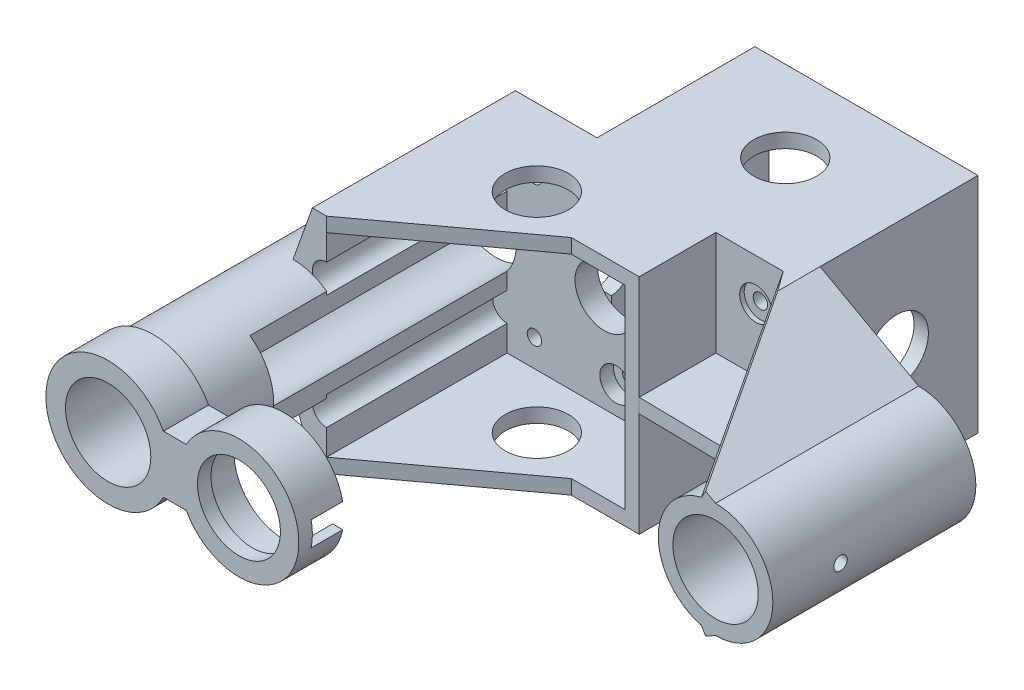
SolidWorks part; units mm, degrees
material "A-Glass Fiber"
ref_plane "Front" through (0, 0, 0) normal (0, 0, 1) x (1, 0, 0)
ref_plane "Top" through (0, 0, 0) normal (0, 1, 0) x (1, 0, 0)
ref_plane "Right" through (0, 0, 0) normal (1, 0, 0) x (0, 0, -1)
sketch "Sketch4" plane through (0, 0, 0) normal (0, 0, 1) x (1, 0, 0)
  line L0 (0, -42.8625) -> (0, 41.275) construction
  line L1 (-49.15, -15.5) -> (-80.15, 15.5) construction
  line L2 (-80.15, -15.5) -> (-49.15, 15.5) construction
  line L3 (-39.925, 44.5615) -> (-39.925, -66.5635) construction
  line L4 (-71.275, 44.5615) -> (-71.275, -66.5635) construction
  line L8 (-62.05, 15.5) -> (-31.05, -15.5) construction
  line L9 (-31.05, 15.5) -> (-62.05, -15.5) construction
  line L11 (-31.05, 36.624) -> (-31.05, -53.8635) construction
  line L12 (43.75, 0) -> (-164.4633, 0) construction
  line L13 (-62.05, 36.624) -> (-62.05, -53.8635) construction
  line L14 (-49.15, 36.624) -> (-49.15, -53.8635) construction
  line L15 (-80.15, 36.624) -> (-80.15, -53.8635) construction
  line L16 (-113.2228, 15.5) -> (-0.2036, 15.5) construction
  line L17 (-113.2228, -15.5) -> (-0.2036, -15.5) construction
  line L18 (-25, -66.5635) -> (-25, 44.5615) construction
  line L19 (-68.1, -66.5635) -> (-68.1, 44.5615) construction
  line L20 (-43.1, 44.5615) -> (-43.1, -66.5635) construction
  line L21 (-86.2, -66.5635) -> (-86.2, 44.5615) construction
  line L22 (5.8397, -21.55) -> (-134.1626, -21.55) construction
  line L23 (5.8397, 21.55) -> (-134.1626, 21.55) construction
  line L24 (10.9249, -24.725) -> (-138.6228, -24.725) construction
  line L25 (10.9249, 24.725) -> (-138.6228, 24.725) construction
  line L26 (-89.375, 44.5615) -> (-89.375, -66.5635) construction
  line L27 (-21.825, 44.5615) -> (-21.825, -66.5635) construction
  circle A0 centre (0, 0) radius 12.7 construction
  circle A1 centre (0, 0) radius 15.875 construction
  circle A2 centre (0, 0) radius 9.46 construction
  circle A3 centre (-93.65, 0) radius 9.46 construction
  arc A4 (-93.65, 12.7) -> (-93.65, -12.7) centre (-93.65, 0) ccw construction
  circle A5 centre (27.27, 0) radius 9.46 construction
  circle A6 centre (27.27, 0) radius 12.7 construction
  circle A7 centre (-120.3675, 0) radius 9.46 construction
  circle A8 centre (-120.3675, 0) radius 12.7 construction
  point P3 (0, 0)
  point P6 (-49.15, -15.5)
  point P11 (-93.65, 0)
  point P12 (-49.15, 15.5)
  point P13 (-46.55, 0)
  point P14 (-80.15, 15.5)
  point P15 (-80.15, -15.5)
  point P61 (-64.65, 0)
  point P65 (27.27, 0)
  point P66 (-120.3675, 0)
  dimension "D20" = 3.175
  dimension "D18" = 29
  dimension "D26" = 73.82
  dimension "D27" = 64.65
  dimension "D2" = 31
  dimension "D3" = 25
  dimension "D4" = 31
  dimension "D5" = 21.825
  dimension "D6" = 15.5
  dimension "D7" = 15.5
  dimension "D8" = 6.05
  dimension "D9" = 6.05
  dimension "D10" = 6.05
  dimension "D11" = 6.05
  dimension "D12" = 6.05
  dimension "D13" = 6.05
  dimension "D14" = 3.175
  dimension "D15" = 3.175
  dimension "D16" = 3.175
  dimension "D17" = 3.175
  dimension "D19" = 3.175
  dimension "D21" = 3.175
  dimension "D22" = 46.55
  dimension "D23" = 47.1
  dimension "D24" = 58.32
  dimension "D25" = 147.6375
sketch "Sketch5" plane through (0, 0, 0) normal (0, 0, 1) x (1, 0, 0)
  line L0 (-21.825, -24.725) -> (0, -12.7)
  line L1 (10.9249, -24.725) -> (-138.6228, -24.725) construction
  line L2 (-21.825, 44.5615) -> (-21.825, -66.5635) construction
  line L3 (0, -42.8625) -> (0, 41.275) construction
  line L4 (10.9249, 24.725) -> (-138.6228, 24.725) construction
  line L5 (-21.825, 24.725) -> (0, 12.7)
  line L6 (-93.65, 0) -> (-93.65, -30.9694) construction
  line L7 (-93.65, 12.7) -> (-89.375, 24.725)
  line L8 (-89.375, 44.5615) -> (-89.375, -66.5635) construction
  line L9 (-89.375, 24.725) -> (-21.825, 24.725)
  line L10 (-89.375, -24.725) -> (-93.65, -12.7)
  line L11 (-89.375, -24.725) -> (-21.825, -24.725)
  circle A0 centre (0, 0) radius 12.7 construction
  arc A1 (0, 12.7) -> (0, -12.7) centre (0, 0) cw
  circle A2 centre (0, 0) radius 9.46
  circle A3 centre (-93.65, 0) radius 9.46
  arc A4 (-93.65, 12.7) -> (-93.65, -12.7) centre (-93.65, 0) ccw
  circle A6 centre (-31.05, 15.5) radius 1.6
  circle A7 centre (-31.05, -15.5) radius 1.6
  circle A8 centre (-49.15, -15.5) radius 1.6
  circle A9 centre (-49.15, 15.5) radius 1.6
  circle A10 centre (-62.05, 15.5) radius 1.6
  circle A11 centre (-80.15, 15.5) radius 1.6
  circle A12 centre (-80.15, -15.5) radius 1.6
  circle A13 centre (-62.05, -15.5) radius 1.6
extrude "Extrude1" add sketch "Sketch5" along normal blind 5
sketch "Sketch6" plane through (0, 0, 5) normal (0, 0, 1) x (1, 0, 0)
  line L0 (-86.2, -21.55) -> (-43.1, -21.55)
  line L1 (-86.2, -66.5635) -> (-86.2, 44.5615) construction
  line L2 (5.8397, -21.55) -> (-134.1626, -21.55) construction
  line L3 (-43.1, 44.5615) -> (-43.1, -66.5635) construction
  line L4 (-43.1, -21.55) -> (-43.1, 21.55)
  line L5 (5.8397, 21.55) -> (-134.1626, 21.55) construction
  line L6 (-43.1, 21.55) -> (-86.2, 21.55)
  line L7 (-39.925, 24.725) -> (-89.375, 24.725)
  line L8 (-93.65, -12.7) -> (-89.375, -24.725) construction
  line L9 (-39.925, 44.5615) -> (-39.925, -66.5635) construction
  line L10 (10.9249, 24.725) -> (-138.6228, 24.725) construction
  line L11 (-12.601, 1.5825) -> (-39.925, 1.5825)
  line L12 (-39.925, -24.725) -> (-89.375, -24.725)
  line L13 (-86.2, 21.55) -> (-86.2, 15.8916)
  line L14 (-86.2, -9.5084) -> (-86.2, -5.83)
  line L15 (-89.375, -24.725) -> (-93.65, -12.7)
  line L16 (-89.375, 24.725) -> (-93.65, 12.7)
  line L19 (-86.2, 9.5416) -> (-86.2, 5.83)
  line L20 (-86.2, -21.55) -> (-86.2, -15.8584)
  line L24 (-39.925, -1.5851) -> (-12.6007, -1.5851)
  line L25 (-39.925, 1.5825) -> (-39.925, 24.725)
  line L27 (-21.825, -24.725) -> (0, -12.7)
  line L28 (-21.825, 24.725) -> (0, 12.7)
  line L29 (-25, 24.725) -> (-3.1127, 12.3127)
  line L30 (-25, -66.5635) -> (-25, 44.5615) construction
  line L31 (-25, -24.725) -> (-3.1127, -12.3127)
  line L32 (10.9249, -24.725) -> (-138.6228, -24.725) construction
  line L33 (-25, -24.725) -> (-21.825, -24.725)
  line L34 (-39.925, -1.5851) -> (-39.925, -24.725)
  line L35 (-25, 24.725) -> (-21.825, 24.725)
  line L36 (0, -42.8625) -> (0, 41.275) construction
  circle A0 centre (-93.65, 0) radius 9.46 construction
  arc A1 (-93.65, 12.7) -> (-93.65, -12.7) centre (-93.65, 0) ccw
  arc A3 (-86.2, 5.83) -> (-86.2, -5.83) centre (-93.65, 0) ccw
  circle A4 centre (0, 0) radius 9.46
  circle A5 centre (0, 0) radius 12.7 construction
  arc A6 (0, -12.7) -> (0, 12.7) centre (0, 0) ccw
  arc A7 (-3.1127, 12.3127) -> (-12.601, 1.5825) centre (0, 0) ccw
  arc A8 (-3.1127, -12.3127) -> (-12.6007, -1.5851) centre (0, 0) cw
  circle A13 centre (-86.2, 12.7166) radius 3.175 construction
  circle A14 centre (-86.2, -12.6834) radius 3.175 construction
  arc A15 (-86.2, 15.8916) -> (-86.2, 9.5416) centre (-86.2, 12.7166) ccw
  arc A16 (-86.2, -9.5084) -> (-86.2, -15.8584) centre (-86.2, -12.6834) ccw
  point P36 (-86.2, 12.7166)
  point P39 (-86.2, -12.6834)
extrude "Extrude2" add sketch "Sketch6" along normal blind 40
sketch "Sketch7" plane through (0, 0, 0) normal (0, 0, -1) x (-1, 0, 0)
  line L0 (68.1, 21.55) -> (25, 21.55)
  line L1 (25, -66.5635) -> (25, 44.5615) construction
  line L2 (-5.8397, -21.55) -> (134.1626, -21.55) construction
  line L3 (25, 21.55) -> (25, -21.55)
  line L4 (68.1, -66.5635) -> (68.1, 44.5615) construction
  line L5 (-5.8397, 21.55) -> (134.1626, 21.55) construction
  line L6 (68.1, 21.55) -> (68.1, -21.55)
  line L7 (68.1, -21.55) -> (25, -21.55)
  line L8 (21.825, 24.725) -> (21.825, -24.725)
  line L9 (21.825, 24.725) -> (71.275, 24.725)
  line L10 (71.275, 44.5615) -> (71.275, -66.5635) construction
  line L11 (-10.9249, 24.725) -> (138.6228, 24.725) construction
  line L12 (71.275, 24.725) -> (71.275, -24.725)
  line L13 (-10.9249, -24.725) -> (138.6228, -24.725) construction
  line L14 (71.275, -24.725) -> (21.825, -24.725)
extrude "Extrude3" add sketch "Sketch7" along normal blind 35
sketch "Sketch12" plane through (4.5259, 7.9808, 0) normal (-0.4933, -0.8699, 0) x (0, 0, 1)
  line L0 (45, 8.7814) -> (5, 33.9433)
  line L1 (5, 33.9433) -> (45, 33.9433)
  line L2 (45, 33.9433) -> (45, 8.7814)
extrude "Extrude5" cut sketch "Sketch12" against normal up to surface (1.5323 mm away)
sketch "Sketch13" plane through (4.5259, -7.9808, 0) normal (-0.4933, 0.8699, 0) x (0, 0, 1)
  line L0 (45, -8.7814) -> (5, -33.9433)
  line L1 (5, -33.9433) -> (45, -33.9433)
  line L2 (45, -33.9433) -> (45, -8.7814)
extrude "Extrude6" cut sketch "Sketch13" against normal up to surface (1.5323 mm away)
sketch "Sketch16" plane through (0, -24.725, 0) normal (0, -1, 0) x (1, 0, 0)
  line L0 (-39.925, 5) -> (-39.925, 22) construction
  line L1 (-39.925, 45) -> (-39.925, 5) construction
  line L2 (-39.925, 22) -> (-16.782, 22.4034)
  line L3 (-16.782, 22.4034) -> (-12.6007, 29.0539)
  line L4 (-12.6007, 45) -> (-12.6007, 5) construction
  line L5 (-12.6007, 29.0539) -> (-12.6007, 45)
  line L6 (-12.6007, 45) -> (-86.2, 45)
  line L7 (-86.2, 45) -> (-54.9816, 22)
  line L8 (-54.9816, 22) -> (-39.925, 22)
  line L9 (-46.55, 0) -> (-46.55, -39.1338) construction
  line L10 (-67.6181, 0) -> (-67.6181, 27.6964) construction
  line L11 (10.9249, 0) -> (-138.6228, 0) construction
  circle A0 centre (-46.55, -17) radius 7
  circle A1 centre (-67.6181, 17) radius 7
extrude "Extrude9" cut sketch "Sketch16" against normal up to surface (49.45 mm away) up to face at (-47.67, 24.725, 3.9695)
sketch "Sketch17" plane through (0, 0, 45) normal (0, 0, 1) x (1, 0, 0)
  line L1 (-86.2, -66.5635) -> (-86.2, 44.5615) construction
  line L2 (-86.2, 10.2853) -> (-86.2, 5.83)
  line L3 (-86.2, -5.83) -> (-86.2, -10.2853)
  arc A0 (-86.2, 5.83) -> (-86.2, -5.83) centre (-93.65, 0) ccw
  arc A1 (-93.65, 12.7) -> (-92.406, -12.6389) centre (-93.65, 0) ccw
  arc A2 (-93.65, 12.7) -> (-93.65, -12.7) centre (-93.65, 0) ccw construction
  arc A3 (-92.406, -12.6389) -> (-86.2, -10.2853) centre (-93.65, 0) ccw
  arc A4 (-93.65, 12.7) -> (-86.2, 10.2853) centre (-93.65, 0) cw
extrude "Extrude10" add sketch "Sketch17" along normal blind 17
sketch "Sketch18" plane through (0, 0, 62) normal (0, 0, 1) x (1, 0, 0)
  circle A0 centre (-93.65, 0) radius 9.46
  circle A1 centre (-93.65, 0) radius 12.7
extrude "Extrude11" add sketch "Sketch18" along normal blind 14
sketch "Sketch19" plane through (0, 0, 76) normal (0, 0, 1) x (1, 0, 0)
  line L0 (-81.3983, -6.3446) -> (-76.3158, -6.3446)
  line L1 (-81.3983, 6.3446) -> (-76.3158, 6.3446)
  circle A0 centre (-64.65, 0) radius 11.1
  circle A1 centre (-64.65, 0) radius 13.2795 construction
  circle A2 centre (-93.65, 0) radius 9.46
  circle A3 centre (-93.65, 0) radius 13.797 construction
  arc A4 (-76.3158, -6.3446) -> (-76.3158, 6.3446) centre (-64.65, 0) ccw
  arc A5 (-81.3983, 6.3446) -> (-81.3983, -6.3446) centre (-93.65, 0) ccw
extrude "Extrude12" add sketch "Sketch19" along normal blind 7
sketch "Sketch20" plane through (0, 0, 83) normal (0, 0, 1) x (1, 0, 0)
  line L1 (-81.3983, -6.3446) -> (-76.3158, -6.3446) construction
  line L2 (-81.3983, -6.3446) -> (-76.3158, -6.3446)
  line L3 (-81.3983, 6.3446) -> (-76.3158, 6.3446)
  circle A0 centre (-93.65, 0) radius 9.46
  circle A1 centre (-93.65, 0) radius 12.7 construction
  circle A2 centre (-64.65, 0) radius 14.39 construction
  arc A3 (-81.3983, 6.3446) -> (-81.3983, -6.3446) centre (-93.65, 0) ccw
  arc A4 (-76.3158, -6.3446) -> (-76.3158, 6.3446) centre (-64.65, 0) ccw
  circle A5 centre (-64.65, 0) radius 9.2
extrude "Extrude13" add sketch "Sketch20" along normal blind 3
sketch "Sketch21" plane through (-43.1, 0, 0) normal (-1, 0, 0) x (0, 0, 1)
  line L0 (76, 0) -> (76, -2.7)
  line L1 (76, 13.797) -> (76, -13.797) construction
  line L2 (76, 0) -> (76, 2.7)
  line L3 (76, -2.7) -> (83, -2.7)
  line L4 (83, 11.1) -> (83, -11.1) construction
  line L5 (83, -2.7) -> (83, 2.7)
  line L6 (83, 2.7) -> (76, 2.7)
extrude "Extrude14" cut sketch "Sketch21" along normal blind 15
sketch "Sketch22" plane through (0, 0, 5) normal (0, 0, 1) x (1, 0, 0)
  circle A0 centre (-62.05, 15.5) radius 3.6
  circle A1 centre (-62.05, -15.5) radius 3.6
extrude "Extrude15" cut sketch "Sketch22" against normal blind 3
sketch "Sketch23" plane through (0, 0, 0) normal (0, 0, -1) x (-1, 0, 0)
  circle A0 centre (49.15, 15.5) radius 3.6
  circle A1 centre (49.15, -15.5) radius 3.6
extrude "Extrude16" cut sketch "Sketch23" against normal blind 3
sketch "Sketch24" plane through (-71.275, 0, 0) normal (-1, 0, 0) x (0, 0, 1)
  line L0 (0, 0) -> (0, 4)
  line L1 (0, -66.5635) -> (0, 44.5615) construction
  line L2 (0, 0) -> (0, -4)
  circle A0 centre (-17, 0) radius 7
  arc A1 (0, 4) -> (0, -4) centre (0, 0) ccw
extrude "Extrude17" cut sketch "Sketch24" against normal up to surface (49.45 mm away) up to face at (-21.825, 0, -17.5)
sketch "Sketch25" plane through (0, 0, 0) normal (0, 0, -1) x (-1, 0, 0)
  circle A0 centre (46.55, 0) radius 6.5
  circle A1 centre (64.65, 0) radius 6.5
extrude "Extrude18" cut sketch "Sketch25" against normal up to surface (5 mm away) up to face at (-58.45, -15.5, 5)
sketch "Sketch26" plane through (-12.6007, 0, 0) normal (-1, 0, 0) x (0, 0, 1)
  line L1 (30, 39.8112) -> (30, -51.0479) construction
  line L2 (0, 44.5615) -> (0, -66.5635) construction
  circle A0 centre (30, 0) radius 1.5
  dimension "D1" = 30
extrude "Extrude19" cut sketch "Sketch26" against normal up to surface and the other way up to surface
sketch "Sketch27" plane through (0, 0, 5) normal (0, 0, 1) x (1, 0, 0)
  circle A0 centre (-31.05, 15.5) radius 3.6
  circle A1 centre (-31.05, -15.5) radius 3.6
extrude "Extrude20" cut sketch "Sketch27" against normal blind 1
